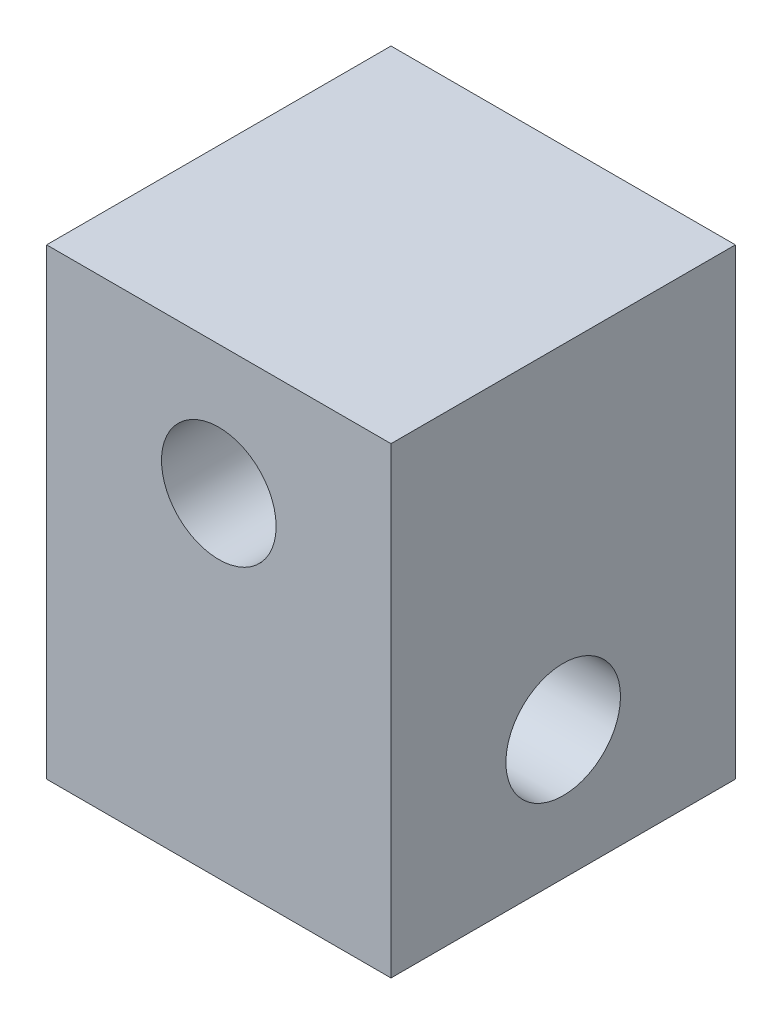
SolidWorks part; units mm, degrees
ref_plane "Front Plane" through (0, 0, 0) normal (0, 0, 1) x (1, 0, 0)
ref_plane "Top Plane" through (0, 0, 0) normal (0, 1, 0) x (1, 0, 0)
ref_plane "Right Plane" through (0, 0, 0) normal (1, 0, 0) x (0, 0, -1)
ref_plane "Plane1" through (-4.064, 0, 0) normal (-1, 0, 0) x (0, -1, 0)
sketch "Sketch1" plane through (-4.064, 0, 0) normal (-1, 0, 0) x (0, -1, 0)
  line L0 (0, 4.064) -> (-10.922, 4.064)
  line L1 (-10.922, 4.064) -> (-10.922, -4.064)
  line L2 (-10.922, -4.064) -> (0, -4.064)
  line L3 (0, -4.064) -> (0, 4.064)
extrude "Boss-Extrude1" add sketch "Sketch1" against normal blind 8.128
hole_wizard "M2.5 Clearance Hole1" positions "Sketch3" profile "Sketch2" hole size "M2.5" standard "ANSI Metric"
sketch "Sketch3" plane through (4.064, 0, 0) normal (1, 0, 0) x (0, 0, -1)
  point P0 (0, 3.048)
sketch "Sketch2" plane through (4.064, 3.048, 0) normal (0, 1, 0) x (0, 0, -1)
  line L0 (0, 0) -> (0, 8.128)
  line L1 (0, 8.128) -> (1.3525, 8.128)
  line L2 (1.3525, 8.128) -> (1.3525, 0)
  line L5 (1.3525, 0) -> (0, 0)
  line L11 (0, -6.35) -> (0, 107.95) construction
  dimension "Thru Hole Dia." = 2.7051
  dimension "Thru Hole Depth" = 8.128
hole_wizard "M2.5 Clearance Hole2" positions "Sketch5" profile "Sketch4" hole size "M2.5" standard "ANSI Metric"
sketch "Sketch5" plane through (0, 0, 4.064) normal (0, 0, 1) x (1, 0, 0)
  point P0 (0, 7.874)
sketch "Sketch4" plane through (0, 7.874, 4.064) normal (1, 0, 0) x (0, -1, 0)
  line L0 (0, 0) -> (0, 8.128)
  line L1 (0, 8.128) -> (1.3525, 8.128)
  line L2 (1.3525, 8.128) -> (1.3525, 0)
  line L5 (1.3525, 0) -> (0, 0)
  line L11 (0, -6.35) -> (0, 107.95) construction
  dimension "Thru Hole Dia." = 2.7051
  dimension "Thru Hole Depth" = 8.128
